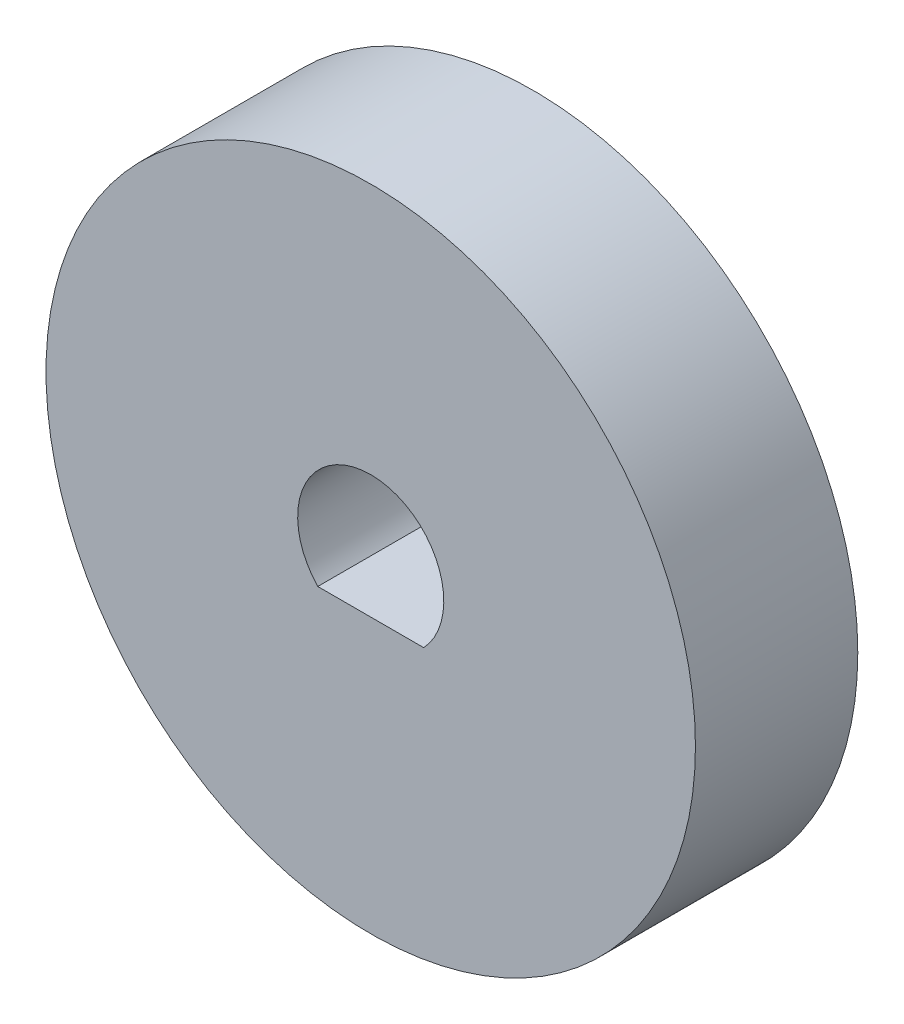
SolidWorks part; units mm, degrees
ref_plane "Спереди" through (0, 0, 0) normal (0, 0, 1) x (1, 0, 0)
ref_plane "Сверху" through (0, 0, 0) normal (0, 1, 0) x (1, 0, 0)
ref_plane "Справа" through (0, 0, 0) normal (1, 0, 0) x (0, 0, -1)
sketch "Эскиз1" plane through (0, 0, 0) normal (0, 0, 1) x (1, 0, 0)
  circle A0 centre (0, 0) radius 10
  dimension "D1" = 20
extrude "Бобышка-Вытянуть2" add sketch "Эскиз1" along normal blind 5
sketch "Эскиз3" plane through (0, 0, 5) normal (0, 0, 1) x (1, 0, 0)
  line L0 (-1.631, -1.55) -> (1.631, -1.55)
  arc A0 (1.631, -1.55) -> (-1.631, -1.55) centre (0, 0) ccw
  dimension "D1" = 4.5
  dimension "D2" = 1.55
extrude "Вырез-Вытянуть2" cut sketch "Эскиз3" against normal blind 5
